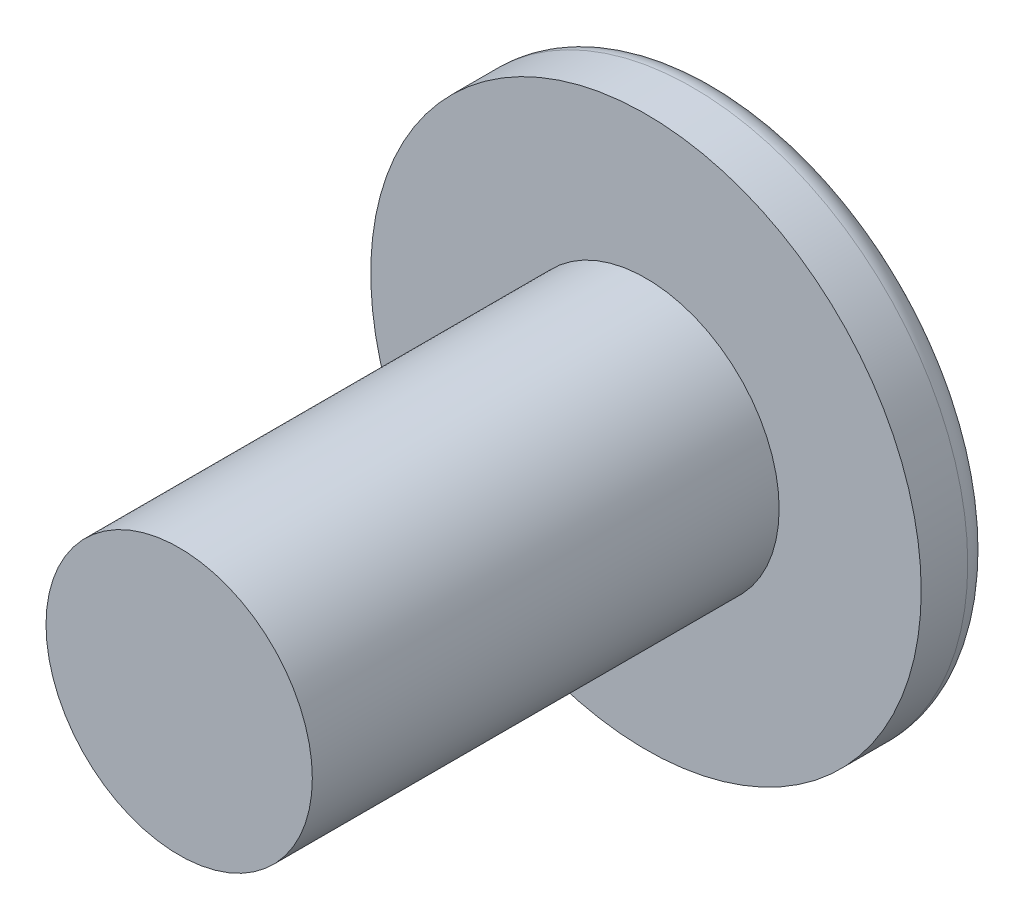
SolidWorks part; units mm, degrees
material "1060 Alloy"
ref_plane "Front Plane" through (0, 0, 0) normal (0, 0, 1) x (1, 0, 0)
ref_plane "Top Plane" through (0, 0, 0) normal (0, 1, 0) x (1, 0, 0)
ref_plane "Right Plane" through (0, 0, 0) normal (1, 0, 0) x (0, 0, -1)
sketch "Sketch1" plane through (0, 0, 0) normal (0, 0, 1) x (1, 0, 0)
  circle A0 centre (0, 0) radius 5.56
  dimension "D1" = 11.12
extrude "Boss-Extrude1" add sketch "Sketch1" along normal blind 1.44
sketch "Sketch2" plane through (0, 0, 1.44) normal (0, 0, 1) x (1, 0, 0)
  circle A0 centre (0, 0) radius 2.69
  dimension "D1" = 5.38
extrude "Boss-Extrude2" add sketch "Sketch2" along normal offset from surface (9.43 mm away) 10.87 up to face at (5.56, 0, 0)
fillet "Fillet1" radius 0.5 1 edges at (5.56, 0, 0)
